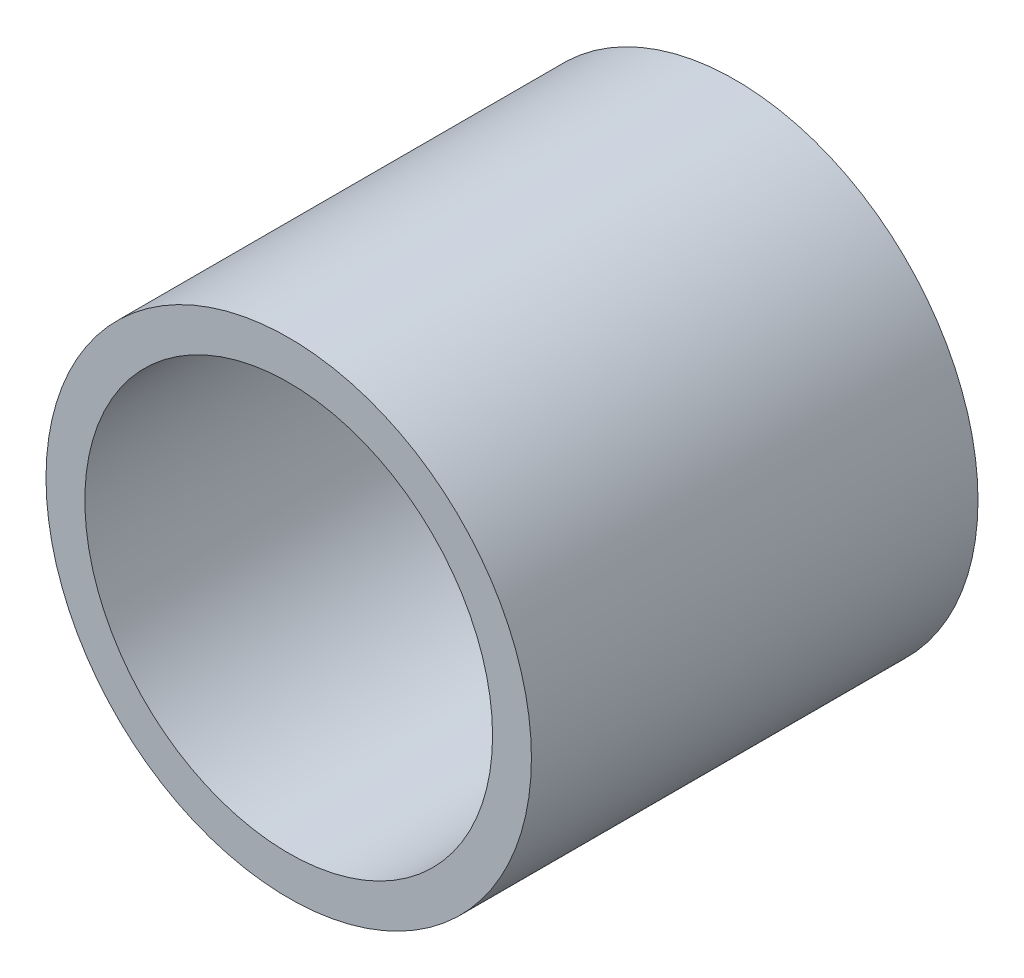
SolidWorks part; units mm, degrees
ref_plane "Front Plane" through (0, 0, 0) normal (0, 0, 1) x (1, 0, 0)
ref_plane "Top Plane" through (0, 0, 0) normal (0, 1, 0) x (1, 0, 0)
ref_plane "Right Plane" through (0, 0, 0) normal (1, 0, 0) x (0, 0, -1)
sketch "Sketch1" plane through (0, 0, 0) normal (0, 0, 1) x (1, 0, 0)
  circle A0 centre (0, 0) radius 12.5
  dimension "D1" = 25
extrude "Boss-Extrude2" add sketch "Sketch1" along normal blind 23
sketch "Sketch3" plane through (0, 0, 23) normal (0, 0, 1) x (1, 0, 0)
  circle A0 centre (0, 0) radius 10.5
  dimension "D1" = 21
extrude "Cut-Extrude1" cut sketch "Sketch3" against normal blind 20
